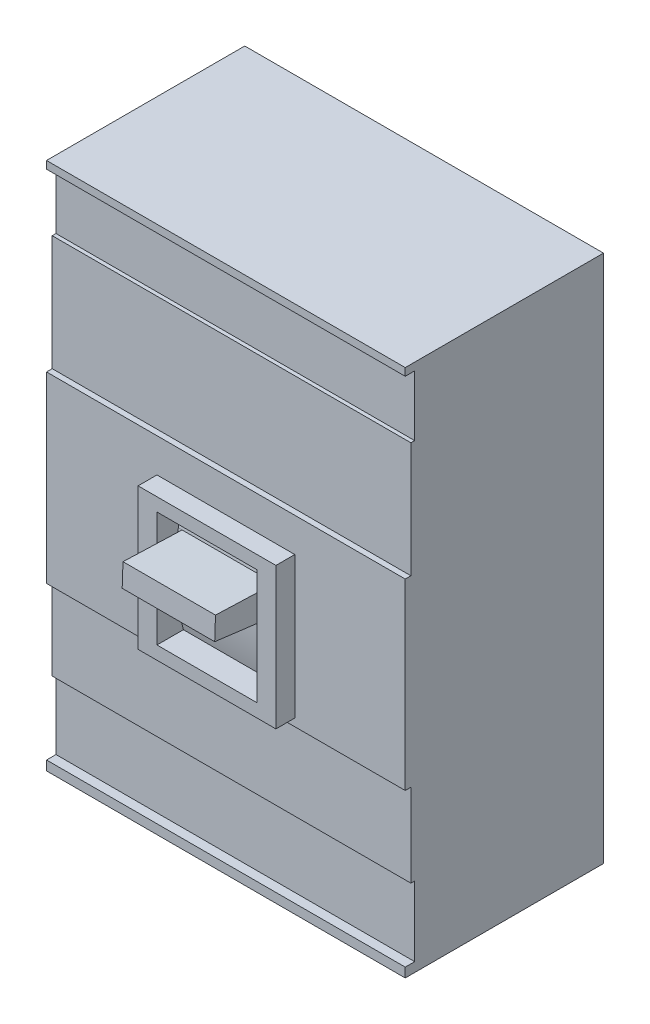
SolidWorks part; units mm, degrees
ref_plane "Alzado" through (0, 0, 0) normal (0, 0, 1) x (1, 0, 0)
ref_plane "Planta" through (0, 0, 0) normal (0, 1, 0) x (1, 0, 0)
ref_plane "Vista lateral" through (0, 0, 0) normal (1, 0, 0) x (0, 0, -1)
sketch "Croquis1" plane through (0, 0, 0) normal (0, 0, 1) x (1, 0, 0)
  line L1 (-95, -140) -> (95, -140)
  line L2 (-95, -140) -> (-95, 140)
  line L3 (-95, 140) -> (95, 140)
  line L4 (95, -140) -> (95, 140)
  line L5 (-95, -140) -> (95, 140) construction
  line L6 (-95, 140) -> (95, -140) construction
  point P0 (0, 0)
  dimension "D1" = 190
  dimension "D2" = 280
extrude "Saliente-Extruir1" add sketch "Croquis1" along normal blind 105
sketch "Croquis2" plane through (0, 0, 105) normal (0, 0, 1) x (1, 0, 0)
  line L0 (95, 140) -> (-95, 140) construction
  line L1 (-36.5, -50) -> (36.5, -50)
  line L2 (-36.5, -50) -> (-36.5, 25)
  line L3 (-36.5, 25) -> (36.5, 25)
  line L4 (36.5, -50) -> (36.5, 25)
  line L5 (-36.5, -50) -> (36.5, 25) construction
  line L6 (-36.5, 25) -> (36.5, -50) construction
  line L7 (95, -140) -> (95, 140) construction
  line L11 (-26.5, -43) -> (26.5, -43)
  line L12 (-26.5, -43) -> (-26.5, 18)
  line L13 (-26.5, 18) -> (26.5, 18)
  line L14 (26.5, -43) -> (26.5, 18)
  line L15 (-26.5, -43) -> (26.5, 18) construction
  line L16 (-26.5, 18) -> (26.5, -43) construction
  point P0 (0, -12.5)
  point P9 (0, -12.5)
  dimension "D1" = 115
  dimension "D2" = 73
  dimension "D3" = 58.5
  dimension "D4" = 75
  dimension "D5" = 10
  dimension "D6" = 7
extrude "Saliente-Extruir2" add sketch "Croquis2" along normal blind 10
sketch "Croquis3" plane through (0, 0, 105) normal (0, 0, 1) x (1, 0, 0)
  line L0 (-95, 104) -> (95, 104)
  line L1 (-95, 140) -> (-95, -140) construction
  line L2 (95, -140) -> (95, 140) construction
  line L3 (95, 140) -> (-95, 140) construction
  line L4 (-95, 136) -> (95, 136)
  line L5 (95, 136) -> (95, 104)
  line L6 (-95, 104) -> (-95, 136)
  dimension "D1" = 36
  dimension "D2" = 4
extrude "Cortar-Extruir1" cut sketch "Croquis3" against normal blind 5
sketch "Croquis4" plane through (0, 0, 105) normal (0, 0, 1) x (1, 0, 0)
  line L0 (-95, 43) -> (95, 43)
  line L1 (-95, 104) -> (-95, -140) construction
  line L2 (95, -140) -> (95, 104) construction
  line L3 (-95, 104) -> (95, 104) construction
  line L4 (-95, 43) -> (-95, 104)
  line L5 (-95, 104) -> (95, 104)
  line L6 (95, 104) -> (95, 43)
  dimension "D1" = 61
extrude "Cortar-Extruir2" cut sketch "Croquis4" against normal blind 3
sketch "Croquis6" plane through (-26.5, 0, 0) normal (1, 0, 0) x (0, 0, -1)
  line L0 (-105, 18) -> (-101, 18)
  line L1 (-105, -43) -> (-101, -43)
  line L2 (-105, 18) -> (-107.9401, -14.9519)
  line L3 (-107.9401, -14.9519) -> (-105, -43)
  arc A0 (-101, -43) -> (-101, 18) centre (13.2812, -12.5) cw
  dimension "D1" = 4
extrude "Cortar-Extruir3" cut sketch "Croquis6" along normal up to surface (53 mm away) up to face at (26.5, -12.5, 110)
sketch "Croquis7" plane through (-26.5, 0, 0) normal (1, 0, 0) x (0, 0, -1)
  line L0 (-103.6815, 5.1119) -> (-135, 6.2132)
  line L1 (-135, 6.2132) -> (-135.4219, -5.7868)
  line L2 (-135.4219, -5.7868) -> (-104.9654, -9.6392)
  line L4 (-115, -50) -> (-115, 25) construction
  arc A0 (-101, 18) -> (-101, -43) centre (13.2812, -12.5) ccw construction
  arc A1 (-104.9654, -9.6392) -> (-103.6815, 5.1119) centre (13.2813, -12.5) cw
  dimension "D1" = 20
  dimension "D2" = 12
extrude "Saliente-Extruir3" add sketch "Croquis7" along normal up to surface (53 mm away) up to face at (26.5, -12.5, 109)
sketch "Croquis8" plane through (26.5, 0, 0) normal (1, 0, 0) x (0, 0, -1)
  line L0 (-135, 6.2132) -> (-103.6815, 5.1119)
  line L1 (-135, 6.2132) -> (-135.4219, -5.7868)
  line L2 (-135.4219, -5.7868) -> (-104.9654, -9.6392)
  arc A0 (-104.9654, -9.6392) -> (-103.6815, 5.1119) centre (-21.8134, -9.4453) cw
extrude "Cortar-Extruir4" cut sketch "Croquis8" against normal blind 2
sketch "Croquis9" plane through (-26.5, 0, 0) normal (-1, 0, 0) x (0, 0, 1)
  line L0 (103.6815, 5.1119) -> (135, 6.2132)
  line L1 (135, 6.2132) -> (135.4219, -5.7868)
  line L2 (135.4219, -5.7868) -> (104.9654, -9.6392)
  arc A0 (104.9654, -9.6392) -> (103.6815, 5.1119) centre (21.8134, -9.4453) ccw
extrude "Cortar-Extruir5" cut sketch "Croquis9" against normal blind 2
sketch "Croquis10" plane through (0, 0, 105) normal (0, 0, 1) x (1, 0, 0)
  line L0 (-95, -54) -> (95, -54)
  line L1 (-95, 43) -> (-95, -140) construction
  line L2 (95, -140) -> (95, 43) construction
  line L3 (-36.5, -50) -> (36.5, -50) construction
  line L4 (-95, -98) -> (95, -98)
  line L5 (-95, -54) -> (-95, -98)
  line L6 (95, -98) -> (95, -54)
  dimension "D1" = 4
  dimension "D2" = 44
extrude "Cortar-Extruir6" cut sketch "Croquis10" against normal blind 3
sketch "Croquis11" plane through (0, 0, 105) normal (0, 0, 1) x (1, 0, 0)
  line L0 (-95, -135) -> (95, -135)
  line L1 (-95, -98) -> (-95, -140) construction
  line L2 (95, -140) -> (95, -98) construction
  line L3 (95, -135) -> (95, -98)
  line L4 (95, -98) -> (-95, -98)
  line L5 (-95, -98) -> (-95, -135)
  dimension "D1" = 5
extrude "Cortar-Extruir7" cut sketch "Croquis11" against normal blind 5
